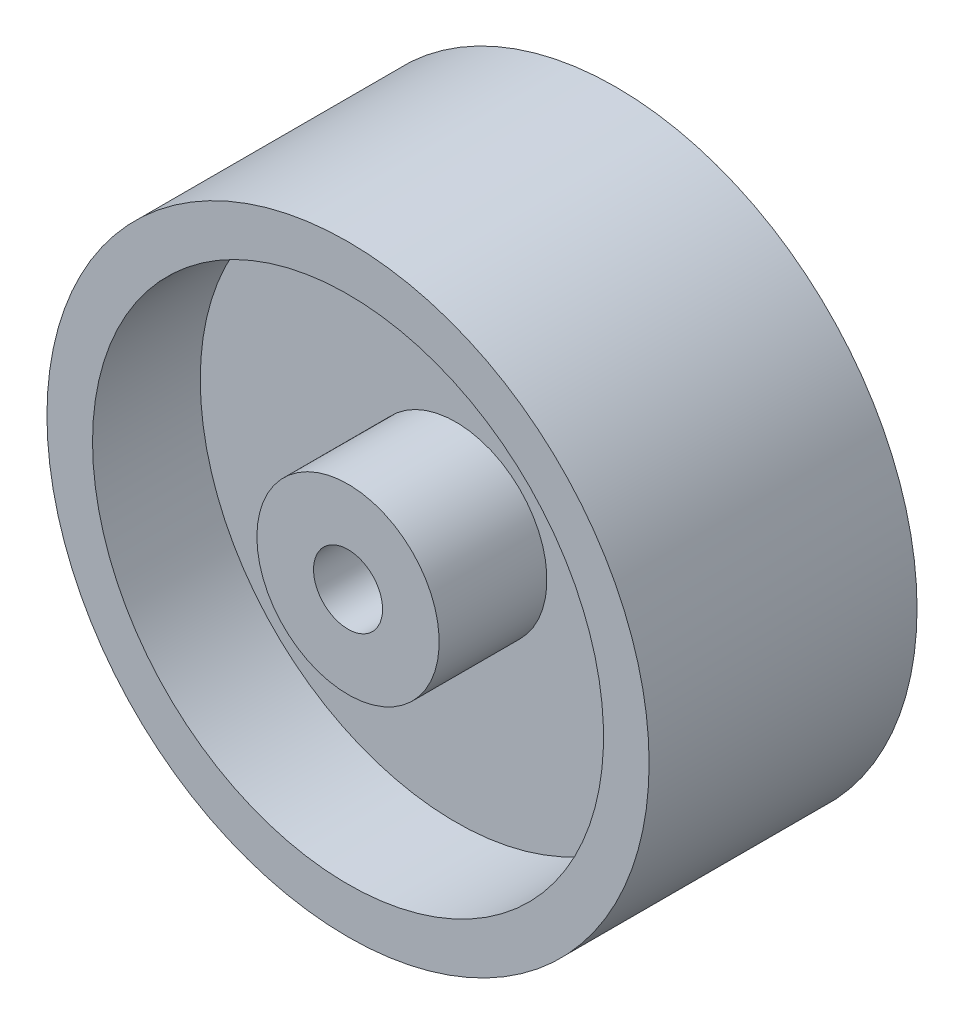
SolidWorks part; units mm, degrees
material "ABS"
ref_plane "Front Plane" through (0, 0, 0) normal (0, 0, 1) x (1, 0, 0)
ref_plane "Top Plane" through (0, 0, 0) normal (0, 1, 0) x (1, 0, 0)
ref_plane "Right Plane" through (0, 0, 0) normal (1, 0, 0) x (0, 0, -1)
sketch "Sketch1" plane through (0, 0, 0) normal (0, 0, 1) x (1, 0, 0)
  circle A0 centre (0, 0) radius 27.686
  dimension "D1" = 55.372
extrude "Boss-Extrude1" add sketch "Sketch1" along normal mid plane 24.638
sketch "Sketch2" plane through (0, 0, 0) normal (1, 0, 0) x (0, 0, -1)
  line L0 (-12.319, 27.686) -> (-12.319, -27.686) construction
  line L1 (-12.319, 23.495) -> (-2.413, 23.495)
  line L2 (-12.319, 23.495) -> (-12.319, 8.382)
  line L3 (-12.319, 8.382) -> (-2.413, 8.382)
  line L4 (-2.413, 23.495) -> (-2.413, 8.382)
  line L5 (12.319, 27.686) -> (-12.319, 27.686) construction
  dimension "D1" = 4.191
  dimension "D2" = 8.382
  dimension "D3" = 9.906
ref_axis "Axis1" through (0, 0, 0) along (0, 0, 1)
revolve "Cut-Revolve1" cut sketch "Sketch2" angle 360 about axis through (0, 0, 0) along (0, 0, 1)
sketch "Sketch3" plane through (0, 0, 12.319) normal (0, 0, 1) x (1, 0, 0)
  circle A0 centre (0, 0) radius 3.175
  dimension "D1" = 6.35
extrude "Cut-Extrude1" cut sketch "Sketch3" against normal through all
mirror "Mirror1" about plane through (0, 0, 0) normal (0, 0, 1) of "Cut-Revolve1"
